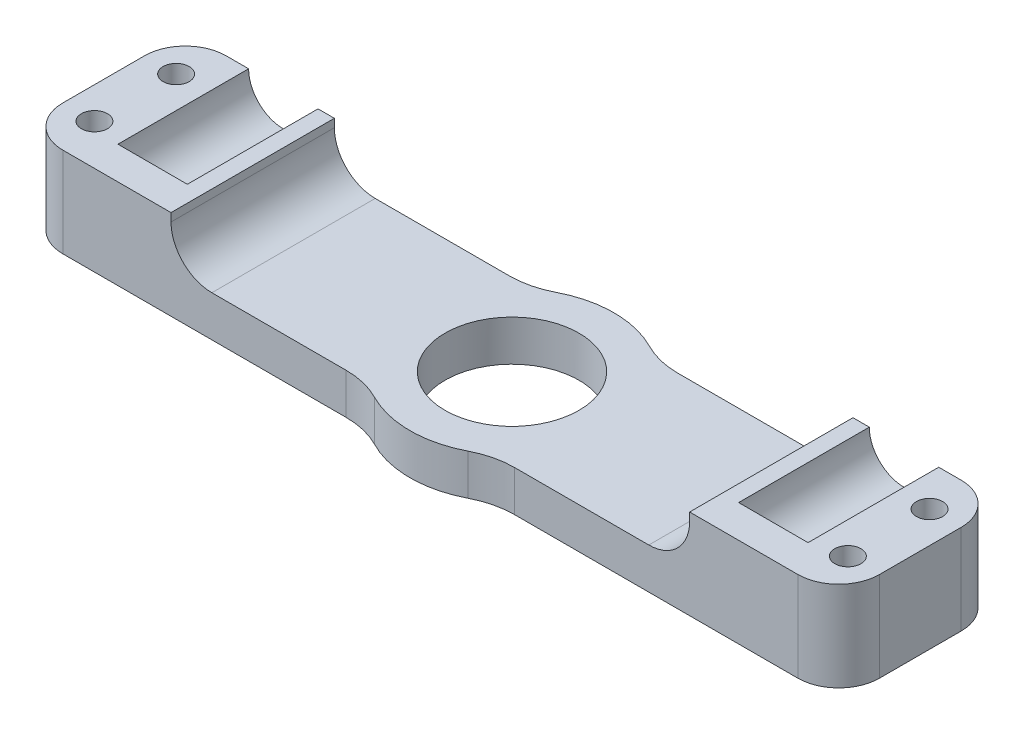
SolidWorks part; units mm, degrees
ref_plane "Front Plane" through (0, 0, 0) normal (0, 0, 1) x (1, 0, 0)
ref_plane "Top Plane" through (0, 0, 0) normal (0, 1, 0) x (1, 0, 0)
ref_plane "Right Plane" through (0, 0, 0) normal (1, 0, 0) x (0, 0, -1)
sketch "Sketch1" plane through (0, 0, 0) normal (0, 1, 0) x (1, 0, 0)
  line L0 (-44, 0) -> (-44, -44) construction
  line L1 (-44, -44) -> (44, -44) construction
  line L2 (44, -44) -> (44, 0) construction
  line L4 (-44, -10) -> (44, -10)
  line L5 (-44, -10) -> (-44, 10)
  line L6 (-44, 10) -> (44, 10)
  line L7 (44, -10) -> (44, 10)
  line L8 (-44, -10) -> (44, 10) construction
  line L9 (-44, 10) -> (44, -10) construction
  arc A0 (44, 0) -> (-44, 0) centre (0, 0) ccw construction
  dimension "D1" = 88
  dimension "D2" = 88
  dimension "D3" = 20
extrude "Boss-Extrude1" add sketch "Sketch1" along normal blind 22
sketch "Sketch2" plane through (0, 0, 10) normal (0, 0, 1) x (1, 0, 0)
  line L1 (-1044, 11) -> (48956, 11) construction
  line L2 (0, -1000) -> (0, 49000) construction
  line L3 (-44, 22) -> (-44, 0) construction
  circle A0 centre (-38, 11) radius 4.25
  circle A1 centre (38, 11) radius 4.25
  point P2 (-44, 11)
  dimension "D1" = 8.5
  dimension "D2" = 6
extrude "Cut-Extrude1" cut sketch "Sketch2" against normal through all
sketch "Sketch7" plane through (0, 22, 0) normal (0, 1, 0) x (1, 0, 0)
  circle A0 centre (0, 0) radius 12.5
  dimension "D1" = 25
extrude "Boss-Extrude2" add sketch "Sketch7" against normal up to surface (22 mm away) up to face at (0, 0, 0)
sketch "Sketch4" plane through (0, 22, 0) normal (0, 1, 0) x (1, 0, 0)
  circle A0 centre (0, 0) radius 8.2
  dimension "D1" = 16.4
extrude "Cut-Extrude3" cut sketch "Sketch4" against normal through all
fillet "Fillet2" radius 10 4 edges at (-7.5, 11, 10) (7.5, 11, 10) (7.5, 11, -10) (-7.5, 11, -10)
sketch "Sketch9" plane through (-44, 0, 0) normal (-1, 0, 0) x (0, 0, 1)
  line L5 (-1017.3065, 22) -> (48982.6935, 22) construction
  line L6 (-1016.9067, 11) -> (48983.0933, 11) construction
  line L7 (-12.5, 22) -> (-12.5, 0) construction
  line L8 (-10, 22) -> (10, 22) construction
  line L9 (12.5, 0) -> (12.5, 22) construction
  line L10 (-13.5, 22) -> (13.5, 22)
  line L11 (-13.5, 22) -> (-13.5, 11)
  line L12 (-13.5, 11) -> (13.5, 11)
  line L13 (13.5, 22) -> (13.5, 11)
  point P3 (-12.5, 11)
  dimension "D1" = 1
  dimension "D2" = 1
extrude "Cut-Extrude4" cut sketch "Sketch9" against normal through all
sketch "Sketch10" plane through (0, 0, 0) normal (0, 0, 1) x (1, 0, 0)
  line L0 (44, 0) -> (10.3078, 0) construction
  line L1 (31.75, 13) -> (-31.75, 13)
  line L2 (31.75, 13) -> (31.75, 5)
  line L3 (31.75, 5) -> (-31.75, 5)
  line L4 (-31.75, 13) -> (-31.75, 5)
  line L5 (10.3078, 11) -> (33.75, 11) construction
  dimension "D1" = 5
  dimension "D2" = 2
  dimension "D3" = 2
  dimension "D4" = 2
extrude "Cut-Extrude5" cut sketch "Sketch10" against normal through all and the other way through all
fillet "Fillet3" radius 5 2 edges at (-31.75, 5, 0) (31.75, 5, 0)
sketch "Sketch11" plane through (44, 0, 0) normal (1, 0, 0) x (0, 0, -1)
  line L4 (10, 0) -> (10, 11)
  line L5 (10, 11) -> (-10, 11)
  line L6 (-10, 11) -> (-10, 0)
  line L7 (-10, 0) -> (10, 0)
  line L8 (10, 0) -> (10, 11)
  line L9 (10, 11) -> (-10, 11)
  line L10 (-10, 11) -> (-10, 0)
  line L11 (-10, 0) -> (10, 0)
  dimension "D1" = 0
extrude "Boss-Extrude3" add sketch "Sketch11" along normal blind 6
sketch "Sketch12" plane through (0, 11, 0) normal (0, 1, 0) x (1, 0, 0)
  line L0 (46.125, -10) -> (46.125, 10) construction
  line L1 (50, -10) -> (42.25, -10) construction
  line L2 (42.25, 10) -> (50, 10) construction
  circle A0 centre (46.125, -5) radius 1.6
  circle A1 centre (46.125, 5) radius 1.6
  dimension "D1" = 3.2
  dimension "D2" = 5
  dimension "D3" = 5
extrude "Cut-Extrude6" cut sketch "Sketch12" against normal through all
mirror "Mirror1" about plane through (0, 0, 0) normal (1, 0, 0) of "Boss-Extrude3", "Cut-Extrude6"
fillet "Fillet4" radius 5 4 edges at (-50, 5.5, 10) (-50, 5.5, -10) (50, 5.5, 10) (50, 5.5, -10)
sketch "Sketch13" plane through (0, 0, 10) normal (0, 0, 1) x (1, 0, 0)
  line L0 (-42.25, 11) -> (-33.75, 11)
  line L1 (33.75, 11) -> (42.25, 11)
  arc A0 (33.75, 11) -> (42.25, 11) centre (38, 11) ccw construction
  arc A1 (-42.25, 11) -> (-33.75, 11) centre (-38, 11) ccw construction
  arc A2 (33.75, 11) -> (42.25, 11) centre (38, 11) ccw
  arc A3 (-42.25, 11) -> (-33.75, 11) centre (-38, 11) ccw
extrude "Boss-Extrude4" add sketch "Sketch13" against normal blind 4
